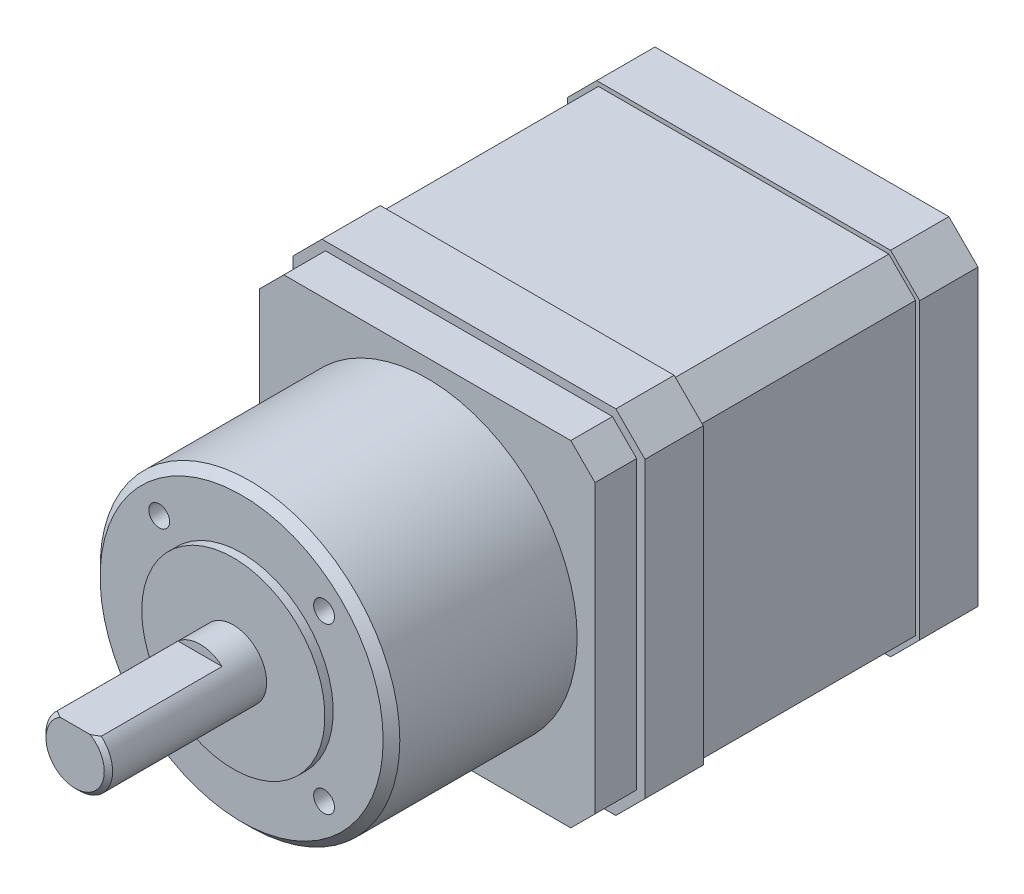
SolidWorks part; units mm, degrees
ref_plane "Ebene vorne" through (0, 0, 0) normal (0, 0, 1) x (1, 0, 0)
ref_plane "Ebene oben" through (0, 0, 0) normal (0, 1, 0) x (1, 0, 0)
ref_plane "Ebene rechts" through (0, 0, 0) normal (1, 0, 0) x (0, 0, -1)
sketch "Skizze1" plane through (0, 0, 0) normal (0, 0, 1) x (1, 0, 0)
  line L1 (21.15, -21.15) -> (-21.15, -21.15)
  line L2 (21.15, -21.15) -> (21.15, 21.15)
  line L3 (21.15, 21.15) -> (-21.15, 21.15)
  line L4 (-21.15, -21.15) -> (-21.15, 21.15)
  line L5 (21.15, -21.15) -> (-21.15, 21.15) construction
  line L6 (21.15, 21.15) -> (-21.15, -21.15) construction
  point P0 (0, 0)
  dimension "D1" = 42.3
extrude "Aufsatz-Linear austragen1" add sketch "Skizze1" along normal blind 40
sketch "Skizze3" plane through (0, 0, 0) normal (1, 0, 0) x (0, 0, -1)
  line L0 (0, 0) -> (-92.6242, 0) construction
  line L1 (-40, 18) -> (-67.3, 18)
  line L2 (-40, -21.15) -> (-40, 21.15) construction
  line L3 (-67.3, 18) -> (-67.3, 11)
  line L4 (-67.3, 11) -> (-68.3, 11)
  line L5 (-68.3, 11) -> (-68.3, 4)
  line L6 (-68.3, 4) -> (-87.3, 4)
  line L7 (-87.3, 4) -> (-87.3, 0)
  line L8 (-87.3, 0) -> (-40, 0)
  line L9 (-40, 0) -> (-40, 18)
  dimension "D1" = 36
  dimension "D2" = 22
  dimension "D3" = 8
  dimension "D4" = 27.3
  dimension "D5" = 1
  dimension "D6" = 20
revolve "Rotation1" add sketch "Skizze3" angle 360 about L0
chamfer "Fase1" distance 3.5 angle 45 4 edges at (21.15, 21.15, 20) (21.15, -21.15, 20) (-21.15, -21.15, 20) (-21.15, 21.15, 20)
sketch "Skizze4" plane through (0, 0, 87.3) normal (0, 0, 1) x (1, 0, 0)
  line L0 (-2.6458, 3) -> (2.6458, 3)
  circle A0 centre (0, 0) radius 4 construction
  arc A1 (2.6458, 3) -> (-2.6458, 3) centre (0, 0) ccw
  point P5 (0, -4)
  dimension "D1" = 7
extrude "Schnitt-Linear austragen1" cut sketch "Skizze4" against normal blind 15
chamfer "Fase2" distance 0.5 angle 45 1 edges at (0, -4, 87.3)
sketch "Skizze5" plane through (0, 0, 40) normal (0, 0, 1) x (1, 0, 0)
  line L44 (20.15, 17.2358) -> (17.2358, 20.15)
  line L45 (20.15, -17.2358) -> (20.15, 17.2358)
  line L46 (17.2358, -20.15) -> (20.15, -17.2358)
  line L47 (-17.2358, -20.15) -> (17.2358, -20.15)
  line L48 (-20.15, -17.2358) -> (-17.2358, -20.15)
  line L49 (-20.15, 17.2358) -> (-20.15, -17.2358)
  line L50 (-17.2358, 20.15) -> (-20.15, 17.2358)
  line L51 (17.2358, 20.15) -> (-17.2358, 20.15)
  line L52 (20.15, 17.2358) -> (17.2358, 20.15)
  line L53 (20.15, -17.2358) -> (20.15, 17.2358)
  line L54 (17.2358, -20.15) -> (20.15, -17.2358)
  line L55 (-17.2358, -20.15) -> (17.2358, -20.15)
  line L56 (-20.15, -17.2358) -> (-17.2358, -20.15)
  line L57 (-20.15, 17.2358) -> (-20.15, -17.2358)
  line L58 (-17.2358, 20.15) -> (-20.15, 17.2358)
  line L59 (17.2358, 20.15) -> (-17.2358, 20.15)
  dimension "D1" = 1
extrude "Aufsatz-Linear austragen2" add sketch "Skizze5" along normal blind 5
hole_wizard "M3 Gewindebohrung1" positions "Skizze7" profile "Skizze6" tap size "M3" standard "ISO"
sketch "Skizze7" plane through (0, 0, 67.3) normal (0, 0, 1) x (1, 0, 0)
  line L1 (-9.8995, 9.8995) -> (0, 0) construction
  line L2 (0, 0) -> (9.8995, 9.8995) construction
  line L4 (9.8995, -9.8995) -> (0, 0) construction
  line L5 (0, 0) -> (-9.8995, -9.8995) construction
  line L7 (0, 0) -> (0, 7.721) construction
  circle A0 centre (0, 0) radius 14 construction
  point P0 (9.8995, 9.8995)
  point P20 (-9.8995, 9.8995)
  point P22 (-9.8995, -9.8995)
  point P24 (9.8995, -9.8995)
  dimension "D1" = 28
  dimension "D2" = 45
sketch "Skizze6" plane through (9.8995, 9.8995, 67.3) normal (1, 0, 0) x (0, -1, 0)
  line L0 (0, 0) -> (0, 5.7511)
  line L1 (0, 5.7511) -> (1.25, 5)
  line L2 (1.25, 5) -> (1.25, 0)
  line L5 (1.25, 0) -> (0, 0)
  line L10 (0, 5.7511) -> (-1.25, 5) construction
  line L11 (0, -6.35) -> (0, 107.95) construction
  dimension "Bohrerdurchmesser" = 2.5
  dimension "Bohrungstiefe" = 5
  dimension "Spitzenwinkel" = 118
cosmetic thread "Bohrungsgewinde1" parameters "D1"=6, "D2"=3
cosmetic thread "Bohrungsgewinde2" parameters "D1"=6, "D2"=3
cosmetic thread "Bohrungsgewinde3" parameters "D1"=6, "D2"=3
cosmetic thread "Bohrungsgewinde4" parameters "D1"=6, "D2"=3
chamfer "Fase3" distance 1 angle 45 1 edges at (-18, 0, 67.3)
sketch "Skizze8" plane through (0, 0, 0) normal (0, 0, -1) x (-1, 0, 0)
  line L16 (17.4429, 20.65) -> (-17.4429, 20.65)
  line L17 (-17.4429, 20.65) -> (-20.65, 17.4429)
  line L18 (-20.65, 17.4429) -> (-20.65, -17.4429)
  line L19 (-20.65, -17.4429) -> (-17.4429, -20.65)
  line L20 (-17.4429, -20.65) -> (17.4429, -20.65)
  line L21 (17.4429, -20.65) -> (20.65, -17.4429)
  line L22 (20.65, -17.4429) -> (20.65, 17.4429)
  line L23 (20.65, 17.4429) -> (17.4429, 20.65)
  line L24 (17.4429, 20.65) -> (-17.4429, 20.65)
  line L25 (-17.4429, 20.65) -> (-20.65, 17.4429)
  line L26 (-20.65, 17.4429) -> (-20.65, -17.4429)
  line L27 (-20.65, -17.4429) -> (-17.4429, -20.65)
  line L28 (-17.4429, -20.65) -> (17.4429, -20.65)
  line L29 (17.4429, -20.65) -> (20.65, -17.4429)
  line L30 (20.65, -17.4429) -> (20.65, 17.4429)
  line L31 (20.65, 17.4429) -> (17.4429, 20.65)
  line L32 (17.65, 21.15) -> (-17.65, 21.15)
  line L33 (-17.65, 21.15) -> (-21.15, 17.65)
  line L34 (-21.15, 17.65) -> (-21.15, -17.65)
  line L35 (-21.15, -17.65) -> (-17.65, -21.15)
  line L36 (-17.65, -21.15) -> (17.65, -21.15)
  line L37 (17.65, -21.15) -> (21.15, -17.65)
  line L38 (21.15, -17.65) -> (21.15, 17.65)
  line L39 (21.15, 17.65) -> (17.65, 21.15)
  line L40 (17.65, 21.15) -> (-17.65, 21.15)
  line L41 (-17.65, 21.15) -> (-21.15, 17.65)
  line L42 (-21.15, 17.65) -> (-21.15, -17.65)
  line L43 (-21.15, -17.65) -> (-17.65, -21.15)
  line L44 (-17.65, -21.15) -> (17.65, -21.15)
  line L45 (17.65, -21.15) -> (21.15, -17.65)
  line L46 (21.15, -17.65) -> (21.15, 17.65)
  line L47 (21.15, 17.65) -> (17.65, 21.15)
  dimension "D1" = 0.5
  dimension "D2" = 0
extrude "Schnitt-Linear austragen2" cut sketch "Skizze8" against normal offset from surface (26 mm away) 7 from offset 7 up to face at (0, 0, 40) offset against normal yes
